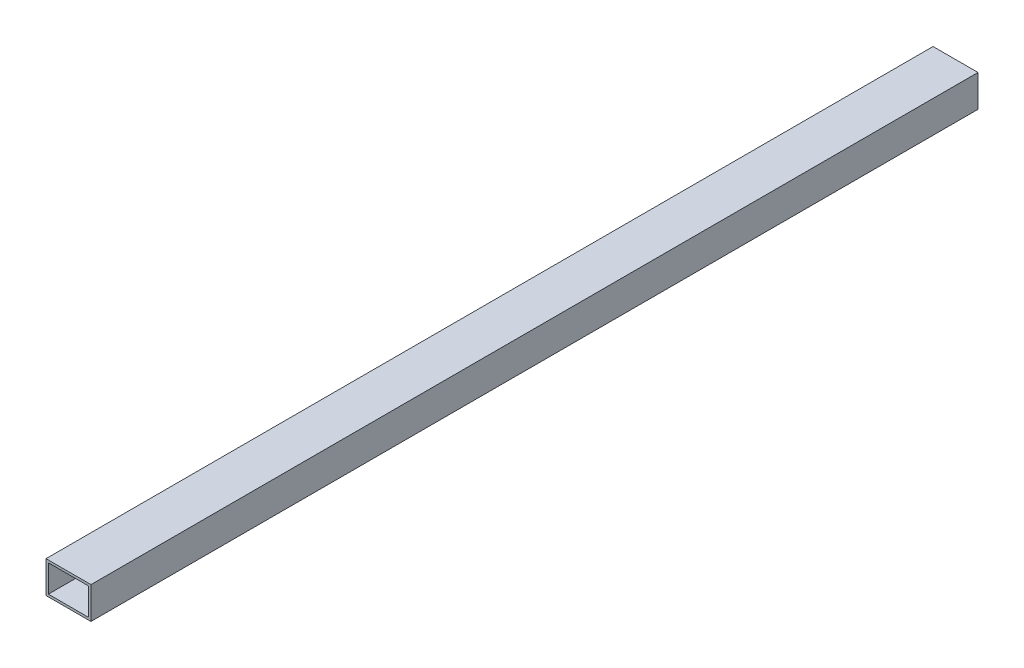
SolidWorks part; units mm, degrees
material "6061 Alloy"
ref_plane "Front Plane" through (0, 0, 0) normal (0, 0, 1) x (1, 0, 0)
ref_plane "Top Plane" through (0, 0, 0) normal (0, 1, 0) x (1, 0, 0)
ref_plane "Right Plane" through (0, 0, 0) normal (1, 0, 0) x (0, 0, -1)
sketch "Sketch1" plane through (0, 0, 0) normal (0, 0, 1) x (1, 0, 0)
  line L0 (-17, 11.5) -> (17, 11.5)
  line L1 (-19, -13.5) -> (19, -13.5)
  line L2 (-19, -13.5) -> (-19, 13.5)
  line L3 (-19, 13.5) -> (19, 13.5)
  line L4 (19, -13.5) -> (19, 13.5)
  line L5 (-19, -13.5) -> (19, 13.5) construction
  line L6 (-19, 13.5) -> (19, -13.5) construction
  line L7 (17, -11.5) -> (17, 11.5)
  line L8 (-17, -11.5) -> (17, -11.5)
  line L9 (-17, -11.5) -> (-17, 11.5)
  point P0 (0, 0)
  dimension "D1" = 38
  dimension "D2" = 27
  dimension "D3" = 2
extrude "Boss-Extrude1" add sketch "Sketch1" along normal blind 750
sketch "Sketch2" plane through (0, 13.5, 0) normal (0, 1, 0) x (1, 0, 0)
  line L0 (-19, -550) -> (19, -550)
  line L1 (-19, -750) -> (-19, 0) construction
  line L2 (19, -750) -> (19, 0) construction
  line L3 (19, -750) -> (-19, -750) construction
  line L4 (-19, -375) -> (19, -375)
  line L5 (-19, -200) -> (19, -200)
  dimension "D1" = 200
  dimension "D2" = 175
